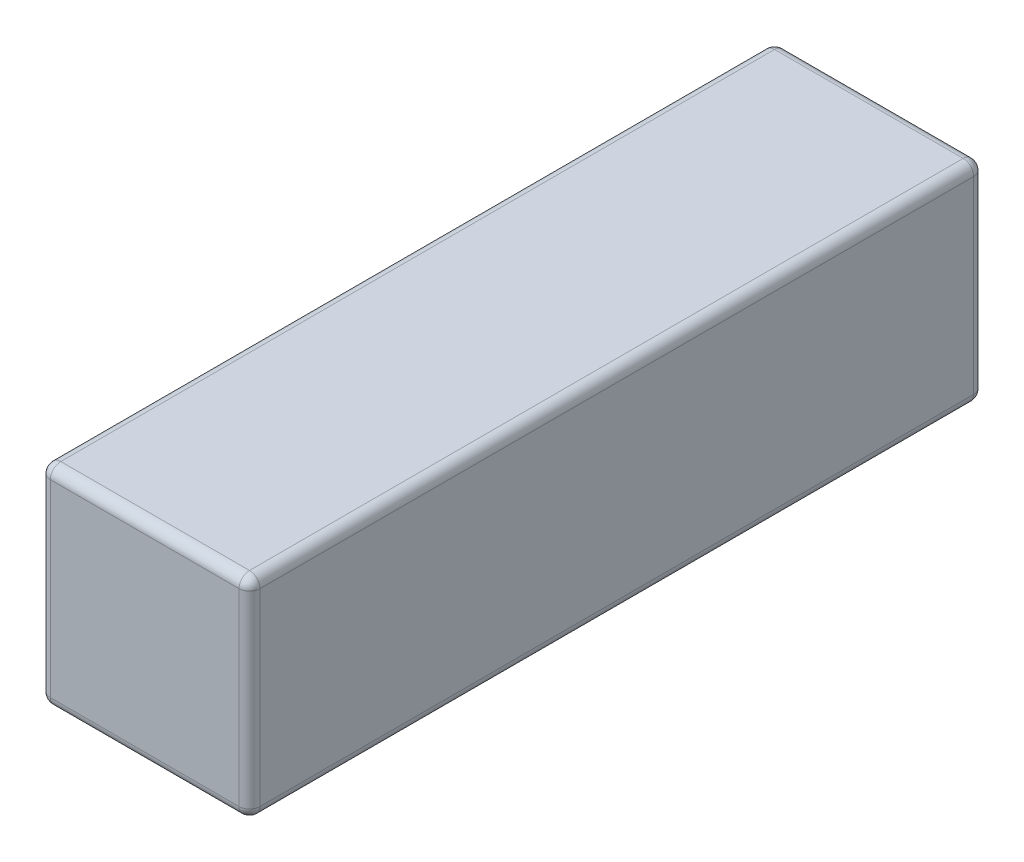
SolidWorks part; units mm, degrees
ref_plane "Front Plane" through (0, 0, 0) normal (0, 0, 1) x (1, 0, 0)
ref_plane "Top Plane" through (0, 0, 0) normal (0, 1, 0) x (1, 0, 0)
ref_plane "Right Plane" through (0, 0, 0) normal (1, 0, 0) x (0, 0, -1)
sketch "Sketch1" plane through (0, 0, 0) normal (0, 0, 1) x (1, 0, 0)
  line L1 (0, 0) -> (25.4, 0)
  line L2 (0, 0) -> (0, 25.4)
  line L3 (0, 25.4) -> (25.4, 25.4)
  line L4 (25.4, 0) -> (25.4, 25.4)
  dimension "D1" = 25.4
  dimension "D2" = 25.4
extrude "Boss-Extrude1" add sketch "Sketch1" along normal blind 89.0016
fillet "Fillet1" radius 1.27 12 edges at (12.7, 0, 0) (25.4, 12.7, 0) (12.7, 25.4, 0) (0, 12.7, 0) (12.7, 25.4, 89.0016) (25.4, 12.7, 89.0016) (12.7, 0, 89.0016) (0, 12.7, 89.0016) (25.4, 0, 44.5008) (0, 0, 44.5008) (0, 25.4, 44.5008) (25.4, 25.4, 44.5008)
